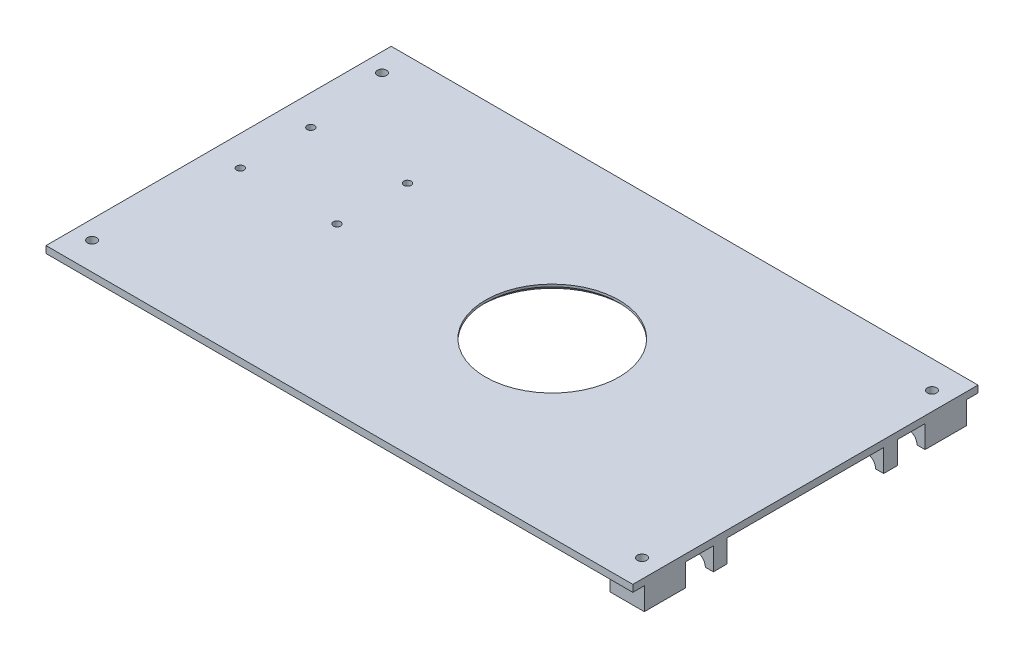
SolidWorks part; units mm, degrees
ref_plane "Front Plane" through (0, 0, 0) normal (0, 0, 1) x (1, 0, 0)
ref_plane "Top Plane" through (0, 0, 0) normal (0, 1, 0) x (1, 0, 0)
ref_plane "Right Plane" through (0, 0, 0) normal (1, 0, 0) x (0, 0, -1)
sketch "Sketch1" plane through (0, 0, 0) normal (0, 1, 0) x (1, 0, 0)
  line L1 (-127.5, -75) -> (127.5, -75)
  line L2 (-127.5, -75) -> (-127.5, 75)
  line L3 (-127.5, 75) -> (127.5, 75)
  line L4 (127.5, -75) -> (127.5, 75)
  line L5 (-127.5, -75) -> (127.5, 75) construction
  line L6 (-127.5, 75) -> (127.5, -75) construction
  point P0 (0, 0)
  dimension "D1" = 255
  dimension "D2" = 150
extrude "Boss-Extrude1" add sketch "Sketch1" along normal blind 3
sketch "Sketch3" plane through (0, 3, 0) normal (0, 1, 0) x (1, 0, 0)
  line L0 (-127.5, 75) -> (-127.5, -75) construction
  circle A0 centre (17.5, 0) radius 29
  dimension "D1" = 58
  dimension "D2" = 145
extrude "Cut-Extrude2" cut sketch "Sketch3" against normal blind 3
sketch "Sketch4" plane through (0, 3, 0) normal (0, 1, 0) x (1, 0, 0)
  circle A0 centre (-72.4213, -3.6409) radius 1.6 construction
  circle A1 centre (-72.4213, 26.9991) radius 1.6 construction
  circle A2 centre (-114.4213, -3.6409) radius 1.6 construction
  circle A3 centre (-114.4213, 26.9991) radius 1.6 construction
  circle A4 centre (-72.4213, -3.6409) radius 1.6
  circle A5 centre (-72.4213, 26.9991) radius 1.6
  circle A6 centre (-114.4213, -3.6409) radius 1.6
  circle A7 centre (-114.4213, 26.9991) radius 1.6
extrude "Cut-Extrude3" cut sketch "Sketch4" against normal up to next
sketch "Sketch5" plane through (0, 0, 0) normal (0, 1, 0) x (1, 0, 0)
  line L1 (-122.4, -55) -> (-107.4, -55)
  line L2 (-122.4, -55) -> (-122.4, -49)
  line L3 (-122.4, -49) -> (-107.4, -49)
  line L4 (-107.4, -55) -> (-107.4, -49)
  line L5 (-127.5, -75) -> (127.5, -75) construction
  line L6 (-127.5, 75) -> (-127.5, -75) construction
  line L7 (-127.5, 0) -> (127.5, 0) construction
  line L8 (127.5, -75) -> (127.5, 75) construction
  dimension "D1" = 20
  dimension "D2" = 6
  dimension "D3" = 15
  dimension "D4" = 5.1
extrude "Boss-Extrude2" add sketch "Sketch5" against normal blind 9.8
sketch "Sketch6" plane through (0, 0, 55) normal (0, 0, 1) x (1, 0, 0)
  line L0 (-122.4, -9.8) -> (-107.4, -9.8) construction
  circle A0 centre (-114.9, -9.8) radius 4
  dimension "D1" = 8
extrude "Cut-Extrude4" cut sketch "Sketch6" against normal up to next
ref_plane "Plane1" through (0, 0, 52) normal (0, 0, 1) x (1, 0, 0)
sketch "Sketch7" plane through (0, 0, 52) normal (0, 0, 1) x (1, 0, 0)
  circle A0 centre (-114.9, -9.8) radius 5
  dimension "D1" = 10
extrude "Cut-Extrude5" cut sketch "Sketch7" against normal mid plane 4
mirror "Mirror1" about plane through (0, 0, 0) normal (0, 0, 1) of "Boss-Extrude2", "Cut-Extrude4", "Cut-Extrude5"
sketch "Sketch8" plane through (0, 0, 0) normal (0, -1, 0) x (1, 0, 0)
  line L0 (127.5, 75) -> (127.5, -75) construction
  line L9 (127.5, -70) -> (112.5, -70)
  line L10 (127.5, -70) -> (127.5, -52)
  line L11 (127.5, -52) -> (112.5, -52)
  line L12 (112.5, -70) -> (112.5, -52)
  line L13 (127.5, -75) -> (-127.5, -75) construction
  line L14 (127.5, -40) -> (112.5, -40)
  line L15 (127.5, -40) -> (127.5, -34)
  line L16 (127.5, -34) -> (112.5, -34)
  line L17 (112.5, -40) -> (112.5, -34)
  dimension "D1" = 5
  dimension "D2" = 18
  dimension "D3" = 12
  dimension "D4" = 6
  dimension "D5" = 15
extrude "Boss-Extrude3" add sketch "Sketch8" along normal blind 9.8
sketch "Sketch9" plane through (0, 0, -34) normal (0, 0, 1) x (1, 0, 0)
  line L0 (127.5, -9.8) -> (112.5, -9.8) construction
  circle A0 centre (120, -9.8) radius 4
  dimension "D1" = 8
extrude "Cut-Extrude6" cut sketch "Sketch9" against normal blind 24
ref_plane "Plane2" through (0, 0, -37) normal (0, 0, 1) x (1, 0, 0)
sketch "Sketch10" plane through (0, 0, -37) normal (0, 0, 1) x (1, 0, 0)
  arc A1 (124, -9.8) -> (116, -9.8) centre (120, -9.8) ccw construction
  circle A2 centre (120, -9.8) radius 5
  arc A3 (124, -9.8) -> (116, -9.8) centre (120, -9.8) ccw
  dimension "D1" = 10
extrude "Cut-Extrude7" cut sketch "Sketch10" against normal mid plane 4 contours A2
pattern_linear "LPattern1" count 2 spacing 18 along (0, 0, -1) of "Cut-Extrude7"
mirror "Mirror2" about plane through (0, 0, 0) normal (0, 0, 1) of "LPattern1", "Cut-Extrude7", "Cut-Extrude6", "Boss-Extrude3"
chamfer "Chamfer1" distance 2 angle 45 1 edges at (17.5, 0, 29)
hole_wizard "Ø4.0mm Dowel Hole1" positions "Sketch11" profile "Sketch12" hole size "Ø4.0" standard "ANSI Metric" end condition through all
sketch "Sketch11" plane through (0, 3, 0) normal (0, 1, 0) x (1, 0, 0)
  line L0 (-127.5, -75) -> (127.5, -75) construction
  line L1 (127.5, -75) -> (127.5, 75) construction
  line L2 (127.5, 75) -> (-127.5, 75) construction
  point P0 (119.5, -63)
  point P2 (119.5, 63)
  dimension "D1" = 12
  dimension "D2" = 8
  dimension "D3" = 8
  dimension "D4" = 12
sketch "Sketch12" plane through (119.5, 3, 63) normal (1, 0, 0) x (0, 0, 1)
  line L0 (0, 0) -> (0, 12.8)
  line L1 (0, 12.8) -> (2, 12.8)
  line L2 (2, 12.8) -> (2, 0)
  line L5 (2, 0) -> (0, 0)
  line L11 (0, -6.35) -> (0, 107.95) construction
  dimension "Thru Hole Dia." = 4
  dimension "Thru Hole Depth" = 12.8
mirror "Mirror3" about plane through (0, 0, 0) normal (1, 0, 0) of "Ø4.0mm Dowel Hole1"
